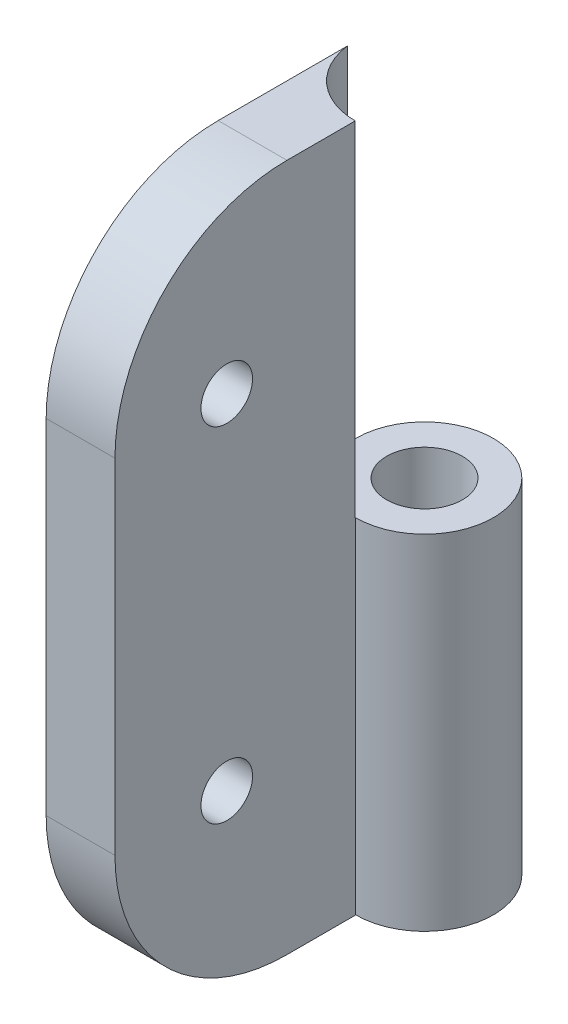
SolidWorks part; units mm, degrees
material "ABS PC"
ref_plane "Front Plane" through (0, 0, 0) normal (0, 0, 1) x (1, 0, 0)
ref_plane "Top Plane" through (0, 0, 0) normal (0, 1, 0) x (1, 0, 0)
ref_plane "Right Plane" through (0, 0, 0) normal (1, 0, 0) x (0, 0, -1)
sketch "Sketch1" plane through (0, 0, 0) normal (0, 0, 1) x (1, 0, 0)
  line L0 (0, 0) -> (0, 40)
extrude "Extrude-Thin2" add sketch "Sketch1" along normal blind 18 thin
sketch "Sketch4" plane through (0, 40, 0) normal (0, 1, 0) x (1, 0, 0)
  circle A0 centre (4, 0) radius 4
sweep "Sweep3" add profiles "Sketch4" path edge at (4, 20, 0)
sketch "Sketch7" plane through (0, 40, 0) normal (0, 1, 0) x (1, 0, 0)
  circle A0 centre (4, 0) radius 2.2
extrude "Cut-Extrude2" cut sketch "Sketch7" against normal through all
sketch "Sketch8" plane through (0, 40, 0) normal (0, 1, 0) x (1, 0, 0)
  circle A0 centre (4, 0) radius 4.03
extrude "Cut-Extrude5" cut sketch "Sketch8" against normal blind 20
sketch "Sketch9" plane through (4, 0, 0) normal (1, 0, 0) x (0, 0, -1)
  line L6 (-18, 0) -> (0, 0) construction
  line L7 (-18, 40) -> (-4.03, 40) construction
  circle A1 centre (-11.5, 10) radius 1.5
  circle A2 centre (-11.5, 30) radius 1.5
  point P0 (-9, 0)
  dimension "D1" = 11.5
  dimension "D2" = 10
  dimension "D3" = 10
extrude "Cut-Extrude6" cut sketch "Sketch9" against normal through all
fillet "Fillet1" radius 10 2 edges at (2, 0, 18) (2, 40, 18)
